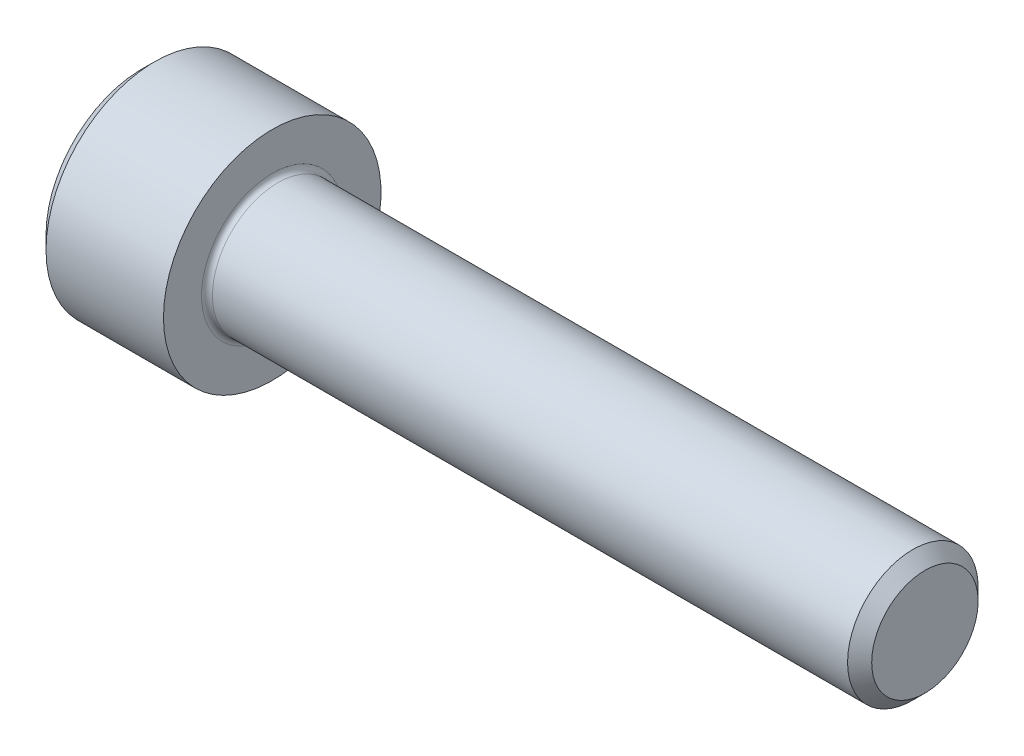
SolidWorks part; units mm, degrees
revolve "Base-Revolve" add sketch "BodySke"
sketch "BodySke" plane through (0, 0, 0) normal (0, 0, 1) x (1, 0, 0)
  line L0 (0, 0) -> (0, 4.4)
  line L1 (0.6, 5) -> (6, 5)
  line L2 (6, 5) -> (6, 3)
  line L3 (6, 3) -> (35.4455, 3)
  line L4 (36, 2.4455) -> (36, 0)
  line L5 (36, 0) -> (0, 0)
  line L6 (-31.75, 0) -> (127, 0) construction
  line L7 (0, 4.4) -> (0.6, 5)
  line L8 (36, 2.4455) -> (35.4455, 3)
  line L9 (0, -4.4) -> (0.6, -5) construction
  line L10 (36, -2.4455) -> (35.4455, -3) construction
  line L11 (7, 9.525) -> (7, 3.175) construction
  line L12 (6, 9.525) -> (6, 3.175) construction
  line L13 (-14, 9.525) -> (-14, 3.175) construction
  dimension "Diameter" = 6
  dimension "Head_ht" = 6
  dimension "Length" = 30
  dimension "Body_ch_ang" = 45
  dimension "Head_dia" = 10
  dimension "Head_ch_ang" = 45
  dimension "Minor_dia" = 4.891
  dimension "Advance" = 1
  dimension "Thread_nom" = 30
  dimension "Thread_length" = 50
  dimension "Head_ch_ht" = 0.6
cosmetic thread "ThreadCosmetic" [suppressed]
fillet "Fillet1" radius 0.25 1 edges at (6, 0, 3)
ref_plane "Plane1" through (0, 0, 0) normal (0, 0, 1) x (1, 0, 0)
ref_plane "Plane2" through (0, 0, 0) normal (0, 1, 0) x (1, 0, 0)
ref_plane "Plane3" through (0, 0, 0) normal (1, 0, 0) x (0, 0, -1)
sketch "Sketch2" plane through (0, 0, 0) normal (0, 0, 1) x (1, 0, 0)
  line L0 (0, 2.542) -> (3, 2.542)
  line L1 (3, 2.542) -> (4.4676, 0)
  line L2 (-31.75, 0) -> (127, 0) construction
  line L3 (4.4676, 0) -> (0, 0)
  line L4 (0, 0) -> (0, 2.542)
  line L5 (0, 4.4) -> (0, -4.4) construction
  line L6 (0, 0) -> (47.625, 0) construction
  line L7 (6, -5) -> (6, 5) construction
  dimension "D1" = 2.542
  dimension "D2" = 60
revolve "Hex-PreBroach" cut sketch "Sketch2" angle 360 about L6
sketch "Sketch3" plane through (0, 0, 0) normal (-1, 0, 0) x (0, 0.5, 0.866)
  line L0 (1.4676, 2.542) -> (-1.4676, 2.542)
  line L1 (-1.4676, 2.542) -> (-2.9352, 0)
  line L2 (1.4676, 2.542) -> (2.9352, 0)
  line L3 (1.4676, -2.542) -> (2.9352, 0)
  line L4 (1.4676, -2.542) -> (-1.4676, -2.542)
  line L5 (-1.4676, -2.542) -> (-2.9352, 0)
  dimension "D1" = 2.542
  dimension "D2" = 2.542
  dimension "Hex_size" = 5.084
extrude "Hex" cut sketch "Sketch3" against normal blind 3
sketch "Sketch4" plane through (0, 0, 0) normal (-1, 0, 0) x (0, 0, 1)
  line L0 (0, 0) -> (2.8067, 0)
  line L1 (0, 0) -> (6.1484, 3.5498) construction
  line L2 (0, 0) -> (1.4033, 2.4307)
  line L3 (2.3336, 0.614) -> (2.6851, 0.817)
  line L4 (1.6986, 1.7139) -> (2.0501, 1.9169)
  arc A0 (2.3336, 0.614) -> (1.6986, 1.7139) centre (0, 0) ccw
  arc A1 (2.8067, 0) -> (2.6851, 0.817) centre (0, 0) ccw
  arc A2 (1.4033, 2.4307) -> (2.0501, 1.9169) centre (0, 0) cw
  dimension "D1" = 30
  dimension "D2" = 60
  dimension "Spline_p_dim" = 1.27
  dimension "D3" = 0.635
extrude "Spline" [suppressed] cut sketch "Sketch4" against normal blind 3
pattern_circular "CirPattern1" [suppressed] count 6 every 60
sketch "Sketch5" plane through (0, 0, 0) normal (0, 0, 1) x (1, 0, 0)
  line L0 (-31.75, 0) -> (127, 0) construction
  line L2 (0, 4.4) -> (0, -4.4) construction
  circle A0 centre (2.3, 0) radius 0.675
  dimension "Drilled_hole_dia" = 1.35
  dimension "Drilled_hole_loc" = 2.3
extrude "Hole" [suppressed] cut sketch "Sketch5" against normal through all and the other way through all
pattern_circular "Drilled-4" [suppressed] count 2 every 60
pattern_circular "Drilled-6" [suppressed] count 3 every 60
sketch "ThdSchSke" plane through (0, 0, 0) normal (0, 0, 1) x (1, 0, 0)
  line L0 (7, -2.4455) -> (6.6117, -3)
  line L1 (7, -2.4455) -> (7.3883, -3)
  line L2 (7.3883, -3) -> (7.3883, -3.75)
  line L3 (-3.175, 0) -> (5.1513, 0) construction
  line L5 (7.3883, -3.75) -> (6.6117, -3.75)
  line L6 (6.6117, -3.75) -> (6.6117, -3)
  line L7 (0, 4.4) -> (0, -4.4) construction
  dimension "Thread_minor" = 4.891
  dimension "Diameter" = 6
  dimension "Start" = 7
revolve "ThreadSchematic" [suppressed] cut sketch "ThdSchSke" angle 360 about L3
pattern_linear "ThdSchPat" [suppressed]
equation "\"D2@Sketch3\" = \"Hex_size@Sketch3\" / 2"
equation "\"D1@Sketch3\" = \"Hex_size@Sketch3\" / 2"
equation "\"D1@Sketch2\" = \"Hex_size@Sketch3\" / 2"
equation "\"D3@Sketch4\" = \"Spline_p_dim@Sketch4\" / 2"
equation "\"Thread_minor@ThreadCosmetic\"  =  \"Minor_dia@BodySke\""
equation "\"D2@CirPattern1\" = 360 / \"Num_teeth@CirPattern1\""
equation "\"Wall_thickness@Sketch2\" = \"Head_ht@BodySke\" - \"Key_eng@Hex\""
equation "\"Thread_length@ThreadCosmetic\" = ((sgn( (\"Length@BodySke\" - \"Advance@BodySke\" ) - \"Thread_nom@BodySke\" )-1)*( (\"Length@BodySke\" - \"Advance@BodySke\" ) - \"Thread_nom@BodySke\" ))/-2+ \"Thread_nom@BodySke\""
equation "\"Thread_minor@ThdSchSke\" = \"Minor_dia@BodySke\""
equation "\"Diameter@ThdSchSke\" = \"Diameter@BodySke\""
equation "\"Overcut@ThdSchSke\" = \"Diameter@BodySke\" * 1.25"
equation "\"Start@ThdSchSke\" = \"Head_ht@BodySke\" + \"Length@BodySke\" - \"Thread_length@ThreadCosmetic\"  '---Non-countersunk---"
equation "\"Num_threads@ThdSchPat\" = int( \"Thread_length@ThreadCosmetic\" / \"Advance@BodySke\" + 0.999 )  + 1"
equation "\"Advance@ThdSchPat\" = \"Thread_length@ThreadCosmetic\" /  (\"Num_threads@ThdSchPat\" - 1) 'relax it"
equation "\"Num_threads@ThdSchPat\" = \"Num_threads@ThdSchPat\" - sgn( \"Num_threads@ThdSchPat\" - 1) '---chamfered tips only---"
